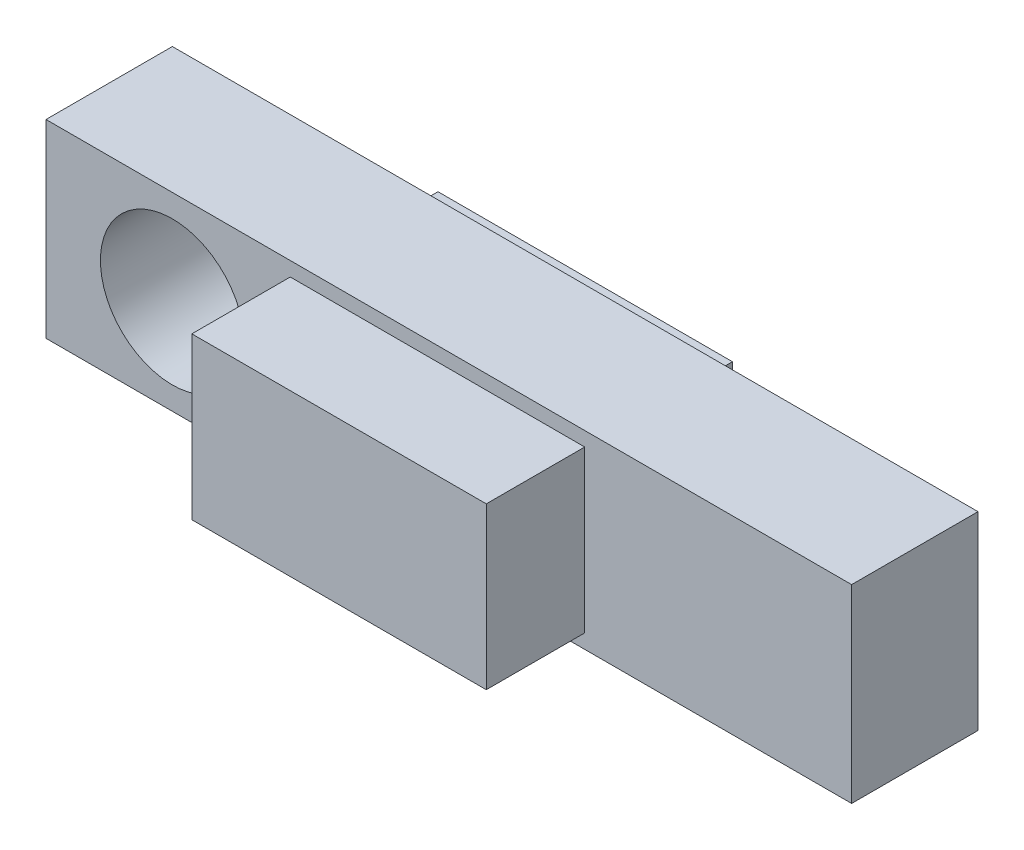
SolidWorks part; units mm, degrees
ref_plane "Front Plane" through (0, 0, 0) normal (0, 0, 1) x (1, 0, 0)
ref_plane "Top Plane" through (0, 0, 0) normal (0, 1, 0) x (1, 0, 0)
ref_plane "Right Plane" through (0, 0, 0) normal (1, 0, 0) x (0, 0, -1)
sketch "Sketch1" plane through (0, 0, 0) normal (0, 0, 1) x (1, 0, 0)
  line L0 (-52.7538, 0) -> (181.7077, 0) construction
  line L1 (0, -19.05) -> (161.925, -19.05)
  line L2 (0, -19.05) -> (0, 19.05)
  line L3 (0, 19.05) -> (161.925, 19.05)
  line L4 (161.925, -19.05) -> (161.925, 19.05)
  dimension "D1" = 38.1
  dimension "D2" = 161.925
extrude "Boss-Extrude1" add sketch "Sketch1" along normal blind 25.4
sketch "Sketch2" plane through (0, 0, 25.4) normal (0, 0, 1) x (1, 0, 0)
  line L0 (0, -19.05) -> (161.925, -19.05) construction
  line L1 (149.6822, -19.05) -> (124.2822, -19.05)
  line L2 (149.6822, -19.05) -> (149.6822, 19.05)
  line L3 (149.6822, 19.05) -> (124.2822, 19.05)
  line L4 (124.2822, -19.05) -> (124.2822, 19.05)
  line L5 (161.925, 19.05) -> (0, 19.05) construction
  line L6 (161.925, -19.05) -> (161.925, 19.05) construction
  dimension "D1" = 25.4
  dimension "D2" = 12.2428
sketch "Sketch3" plane through (0, 0, 25.4) normal (0, 0, 1) x (1, 0, 0)
  line L0 (0, 0) -> (183.5422, 0) construction
  line L1 (49.0982, -16.1798) -> (108.2802, -16.1798)
  line L2 (49.0982, -16.1798) -> (49.0982, 16.1798)
  line L3 (49.0982, 16.1798) -> (108.2802, 16.1798)
  line L4 (108.2802, -16.1798) -> (108.2802, 16.1798)
  line L5 (0, 19.05) -> (0, -19.05) construction
  line L6 (161.925, 19.05) -> (0, 19.05) construction
  dimension "D1" = 49.0982
  dimension "D2" = 2.8702
  dimension "D3" = 59.182
extrude "Boss-Extrude3" add sketch "Sketch3" along normal blind 19.7866
sketch "Sketch4" plane through (0, 0, 0) normal (0, 0, -1) x (-1, 0, 0)
  line L2 (-49.0982, 16.1798) -> (-108.2802, 16.1798)
  line L3 (-49.0982, 16.1798) -> (-49.0982, -16.1798)
  line L4 (-49.0982, -16.1798) -> (-108.2802, -16.1798)
  line L5 (-108.2802, 16.1798) -> (-108.2802, -16.1798)
extrude "Boss-Extrude4" add sketch "Sketch4" along normal blind 4.2926
sketch "Sketch6" plane through (0, 0, 25.4) normal (0, 0, 1) x (1, 0, 0)
  line L0 (0, 19.05) -> (0, -19.05) construction
  line L1 (0, 0) -> (161.925, 0) construction
  line L2 (161.925, -19.05) -> (161.925, 19.05) construction
  circle A0 centre (25.4, 0) radius 14.4653
  dimension "D2" = 28.9306
  dimension "D1" = 25.4
extrude "Cut-Extrude1" cut sketch "Sketch6" against normal through all
